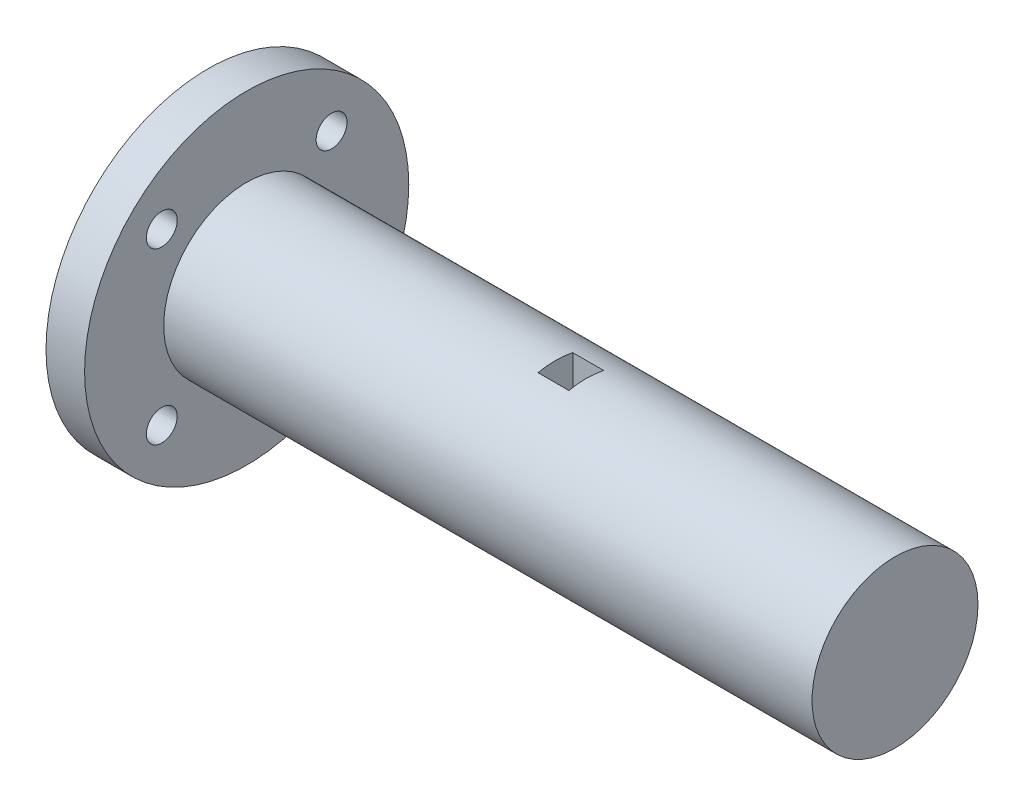
SolidWorks part; units mm, degrees
ref_plane "Piano frontale" through (0, 0, 0) normal (0, 0, 1) x (1, 0, 0)
ref_plane "Piano superiore" through (0, 0, 0) normal (0, 1, 0) x (1, 0, 0)
ref_plane "Piano destro" through (0, 0, 0) normal (1, 0, 0) x (0, 0, -1)
sketch "Sketch1" plane through (0, 0, 0) normal (1, 0, 0) x (0, 0, -1)
  circle A3 centre (0, 0) radius 10.75
  dimension "D1" = 21.5
extrude "Boss-Extrude1" add sketch "Sketch1" along normal blind 40
sketch "Sketch4" plane through (0, 0, 0) normal (-1, 0, 0) x (0, 0, 1)
  line L0 (0, 11) -> (0, -11) construction
  line L1 (-11, 11) -> (11, 11) construction
  line L2 (-11, 11) -> (-11, -11) construction
  line L3 (-11, -11) -> (11, -11) construction
  line L4 (11, 11) -> (11, -11) construction
  line L5 (-11, 0) -> (11, 0) construction
  circle A0 centre (0, 0) radius 21
  circle A1 centre (0, 0) radius 10.75 construction
  circle A4 centre (-11, 11) radius 2
  circle A5 centre (11, 11) radius 2
  circle A6 centre (11, -11) radius 2
  circle A7 centre (-11, -11) radius 2
  point P23 (0, -11)
  point P31 (0, 0)
  dimension "D1" = 42
  dimension "D2" = 4
  dimension "D3" = 22
  dimension "D4" = 22
extrude "Boss-Extrude3" add sketch "Sketch4" along normal blind 5
sketch "Sketch6" plane through (40, 0, 0) normal (1, 0, 0) x (0, 0, -1)
  line L1 (-2.25, 6.5119) -> (2.25, 6.5119)
  line L2 (-2.25, 6.5119) -> (-2.25, 10.5119)
  line L4 (2.25, 6.5119) -> (2.25, 10.5119)
  arc A0 (-2.25, 10.5119) -> (2.25, 10.5119) centre (0, 0) ccw
  point P7 (0, 6.5119)
  dimension "D3" = 21.5
  dimension "D1" = 4
  dimension "D2" = 4.5
extrude "Boss-Extrude5" add sketch "Sketch6" along normal blind 4
sketch "Sketch7" plane through (44, 0, 0) normal (1, 0, 0) x (0, 0, -1)
  circle A0 centre (0, 0) radius 10.75
extrude "Boss-Extrude6" add sketch "Sketch7" along normal blind 40
